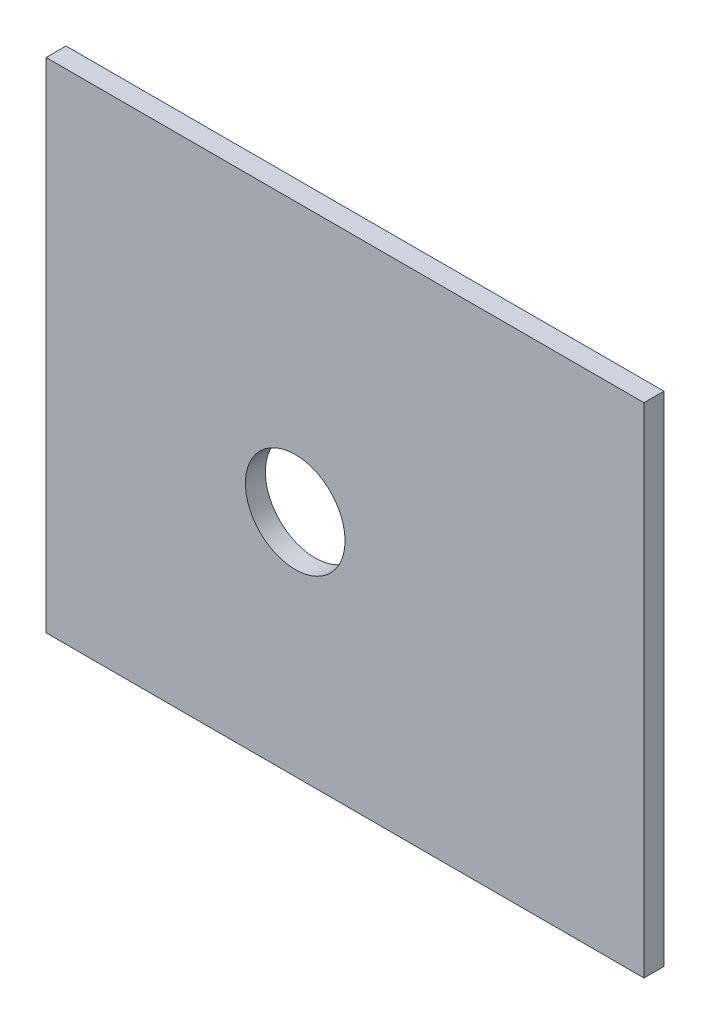
SolidWorks part; units mm, degrees
ref_plane "Front Plane" through (0, 0, 0) normal (0, 0, 1) x (1, 0, 0)
ref_plane "Top Plane" through (0, 0, 0) normal (0, 1, 0) x (1, 0, 0)
ref_plane "Right Plane" through (0, 0, 0) normal (1, 0, 0) x (0, 0, -1)
sketch "Sketch1" plane through (0, 0, 0) normal (0, 0, 1) x (1, 0, 0)
  line L1 (-30, 25) -> (30, 25)
  line L2 (-30, 25) -> (-30, -25)
  line L3 (-30, -25) -> (30, -25)
  line L4 (30, 25) -> (30, -25)
  line L5 (-30, 25) -> (30, -25) construction
  line L6 (-30, -25) -> (30, 25) construction
  circle A0 centre (-5, -2) radius 5
  point P0 (-5, -2)
  dimension "D3" = 10
  dimension "D1" = 50
  dimension "D2" = 60
  dimension "D4" = 2
  dimension "D5" = 5
extrude "Boss-Extrude1" add sketch "Sketch1" along normal blind 2
